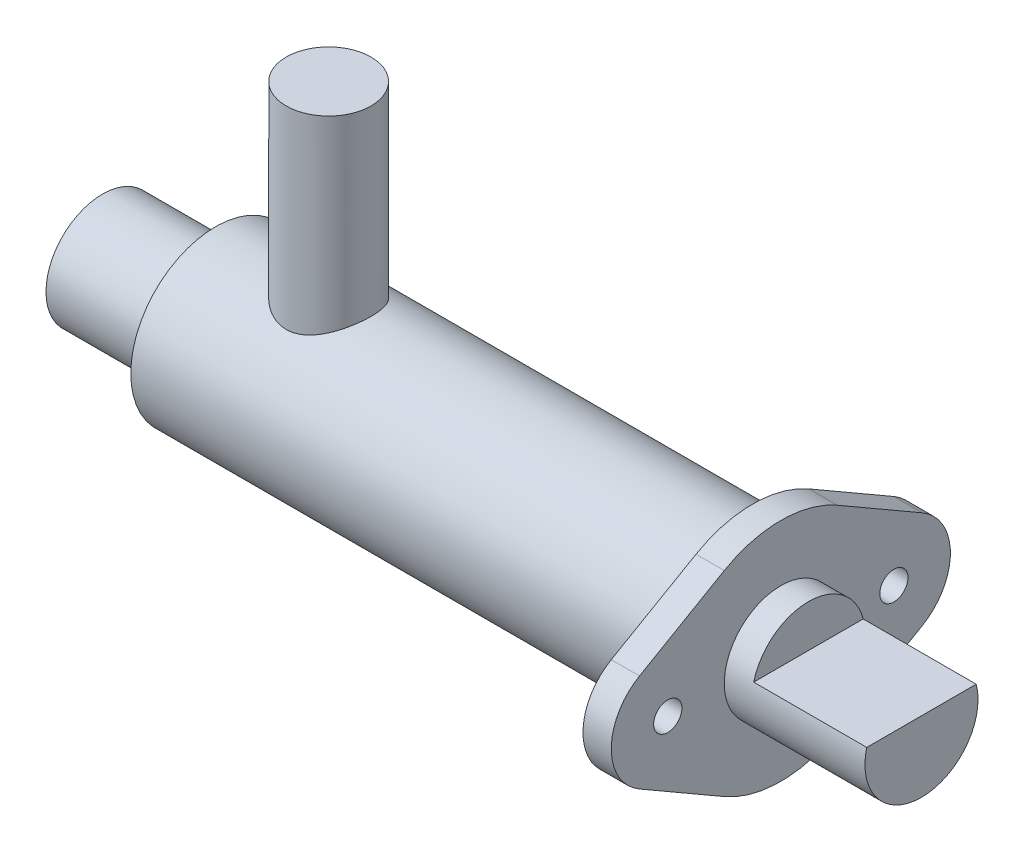
SolidWorks part; units mm, degrees
material "3003 Alloy"
ref_plane "Front" through (0, 0, 0) normal (0, 0, 1) x (1, 0, 0)
ref_plane "Top" through (0, 0, 0) normal (0, 1, 0) x (1, 0, 0)
ref_plane "Right" through (0, 0, 0) normal (1, 0, 0) x (0, 0, -1)
sketch "Sketch3" plane through (0, 0, 0) normal (0, 0, 1) x (1, 0, 0)
  circle A0 centre (0, 0) radius 5.5562
sketch "Sketch6" plane through (0, 0, 0) normal (1, 0, 0) x (0, -1, 0)
  circle A0 centre (0, 0) radius 4.7625
sketch "Sketch4" plane through (0, 0, 0) normal (0, 0, 1) x (1, 0, 0)
  line L0 (-47.625, 0) -> (66.675, 0) construction
  line L1 (-47.625, 0) -> (-47.625, -6.35)
  line L2 (-47.625, -6.35) -> (-34.925, -6.35)
  line L3 (-34.925, -6.35) -> (-34.925, -9.525)
  line L4 (-34.925, -9.525) -> (28.575, -9.525)
  line L5 (28.575, 0) -> (28.575, -9.525)
  line L6 (-47.625, 0) -> (28.575, 0)
revolve "Boss-Revolve2" add sketch "Sketch4" angle 360 about L0
sketch "Sketch5" plane through (28.575, 0, 0) normal (1, 0, 0) x (0, 0, -1)
  circle A0 centre (0, 0) radius 6.35
  dimension "D1" = 12.7
sketch "Sketch7" plane through (28.575, 29.3187, 10.1742) normal (1, 0, 0) x (0, 0.7071, -0.7071)
  line L0 (-13.5372, -27.9258) -> (12.2142, -2.1743) construction
  line L1 (43.6677, 29.2792) -> (-70.7421, -85.1307) construction
  line L2 (-20.874, -12.8119) -> (-10.2502, -15.6585)
  line L3 (-28.6511, -20.589) -> (-25.8045, -31.2128)
  line L4 (-22.5175, -18.9455) -> (-4.5569, -36.906) construction
  line L5 (-6.2004, -43.0396) -> (-16.8242, -40.193)
  line L6 (1.5767, -35.2625) -> (-1.2699, -24.6388)
  arc A0 (-28.6511, -20.589) -> (-20.874, -12.8119) centre (-22.5175, -18.9455) cw
  arc A1 (-6.2004, -43.0396) -> (1.5767, -35.2625) centre (-4.5569, -36.906) ccw
  arc A2 (-1.2699, -24.6388) -> (-10.2502, -15.6585) centre (-13.5372, -27.9258) ccw
  arc A3 (-25.8045, -31.2128) -> (-16.8242, -40.193) centre (-13.5372, -27.9258) ccw
  circle A4 centre (-22.5175, -18.9455) radius 1.5875
  circle A5 centre (-4.5569, -36.906) radius 1.5875
  circle A6 centre (-13.5372, -27.9258) radius 9.525 construction
  dimension "D2" = 25.4
  dimension "D3" = 6.35
  dimension "D5" = 12.7
  dimension "D6" = 12.7
  dimension "D1" = 3.175
extrude "Boss-Extrude2" add sketch "Sketch7" against normal blind 3.175
extrude "Cut-Extrude1" cut sketch "Sketch5" against normal blind 41.3489
sketch "Sketch8" plane through (-12.7739, 0, 0) normal (1, 0, 0) x (0, 0, -1)
  circle A1 centre (0, 0) radius 6.35
  circle A2 centre (0, 0) radius 6.35
  dimension "D1" = 0
extrude "Extrude1" add sketch "Sketch8" along normal blind 57.15
sketch "Sketch9" plane through (44.3761, 0, 0) normal (1, 0, 0) x (0, 0, -1)
  line L0 (-6.1484, 1.5875) -> (6.1484, 1.5875)
  circle A0 centre (0, 0) radius 6.35 construction
  arc A1 (6.1484, 1.5875) -> (-6.1484, 1.5875) centre (0, 0) ccw
  dimension "D1" = 1.5875
extrude "Cut-Extrude2" cut sketch "Sketch9" against normal blind 12.7
sketch "Sketch10" plane through (0, 0, 0) normal (0, 1, 0) x (1, 0, 0)
  line L1 (-34.925, 9.525) -> (-34.925, -9.525) construction
  circle A0 centre (-22.225, 0) radius 4.7625
  dimension "D1" = 9.525
  dimension "D2" = 12.7
extrude "Extrude2" add sketch "Sketch10" along normal blind 30
